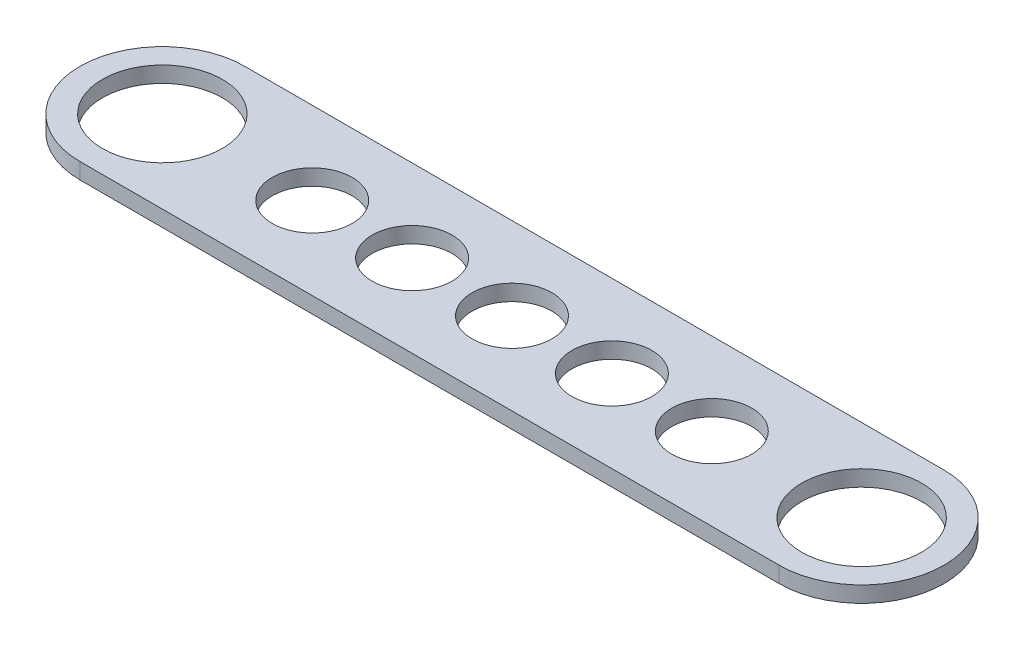
SolidWorks part; units mm, degrees
ref_plane "Front Plane" through (0, 0, 0) normal (0, 0, 1) x (1, 0, 0)
ref_plane "Top Plane" through (0, 0, 0) normal (0, 1, 0) x (1, 0, 0)
ref_plane "Right Plane" through (0, 0, 0) normal (1, 0, 0) x (0, 0, -1)
sketch "Sketch1" plane through (0, 0, 0) normal (0, 1, 0) x (1, 0, 0)
  line L0 (0, 0) -> (177.8, 0) construction
  line L1 (0, 20.955) -> (177.8, 20.955)
  line L2 (0, -20.955) -> (177.8, -20.955)
  arc A0 (0, 20.955) -> (0, -20.955) centre (0, 0) ccw
  arc A1 (177.8, -20.955) -> (177.8, 20.955) centre (177.8, 0) ccw
  circle A2 centre (0, 0) radius 15.24
  circle A3 centre (177.8, 0) radius 15.24
  point P3 (88.9, 0)
  dimension "D3" = 30.48
  dimension "D4" = 30.48
  dimension "D1" = 41.91
  dimension "D2" = 177.8
extrude "Boss-Extrude1" add sketch "Sketch1" along normal blind 4.064
sketch "Sketch2" plane through (0, 4.064, 0) normal (0, 1, 0) x (1, 0, 0)
  circle A0 centre (38.1, 0) radius 10.16
  circle A1 centre (0, 0) radius 15.24 construction
  dimension "D1" = 20.32
  dimension "D2" = 38.1
extrude "Cut-Extrude1" cut sketch "Sketch2" against normal through all
pattern_linear "LPattern1" count 5 spacing 25.4 along (1, 0, 0) of "Cut-Extrude1"
